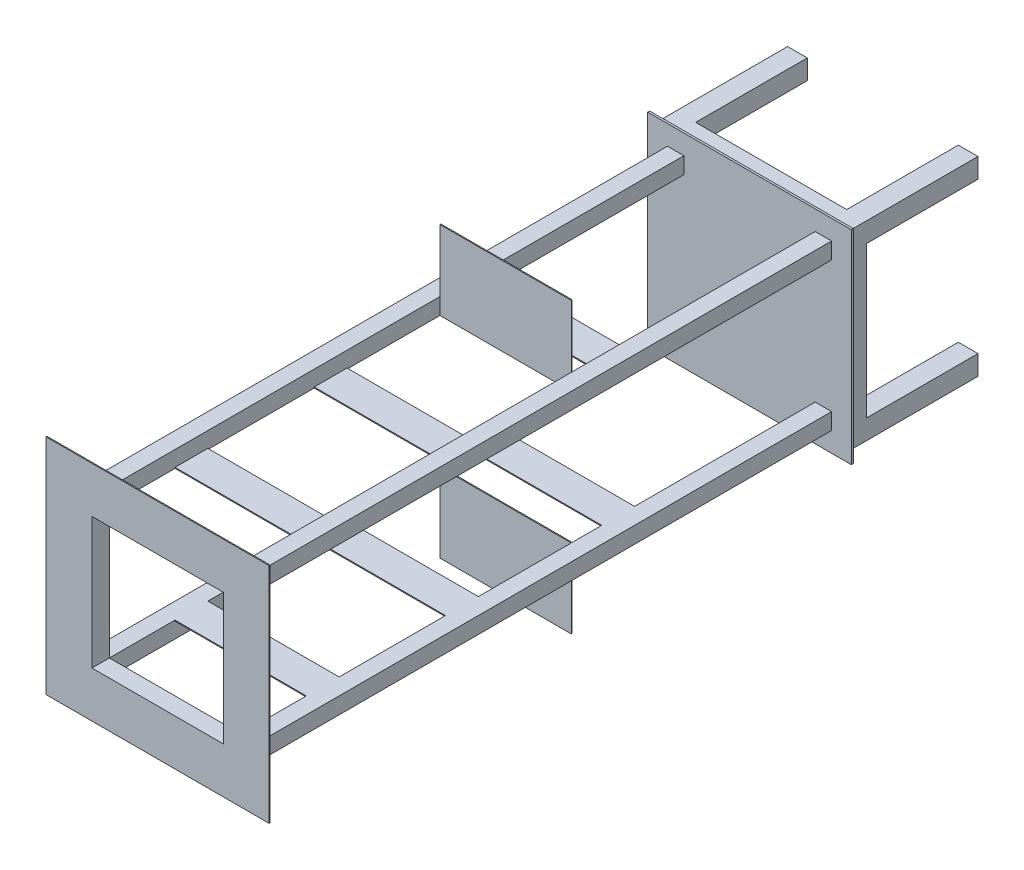
SolidWorks part; units mm, degrees
material "可鍛鑄鐵"
ref_plane "前基準面" through (0, 0, 0) normal (0, 0, 1) x (1, 0, 0)
ref_plane "上基準面" through (0, 0, 0) normal (0, 1, 0) x (1, 0, 0)
ref_plane "右基準面" through (0, 0, 0) normal (1, 0, 0) x (0, 0, -1)
other "質量中心"
sketch "草圖1" plane through (0, 0, 0) normal (0, 0, 1) x (1, 0, 0)
  line L0 (-96.0687, 115.7874) -> (-70.0687, 115.7874)
  line L1 (-98.0687, 117.7874) -> (-68.0687, 117.7874)
  line L2 (-98.0687, 117.7874) -> (-98.0687, 87.7874)
  line L3 (-98.0687, 87.7874) -> (-68.0687, 87.7874)
  line L4 (-68.0687, 117.7874) -> (-68.0687, 87.7874)
  line L5 (-70.0687, 115.7874) -> (-70.0687, 89.7874)
  line L6 (-96.0687, 89.7874) -> (-70.0687, 89.7874)
  line L7 (-96.0687, 115.7874) -> (-96.0687, 89.7874)
  line L8 (163.9313, 115.7874) -> (189.9313, 115.7874)
  line L9 (161.9313, 117.7874) -> (191.9313, 117.7874)
  line L10 (161.9313, 117.7874) -> (161.9313, 87.7874)
  line L11 (161.9313, 87.7874) -> (191.9313, 87.7874)
  line L12 (191.9313, 117.7874) -> (191.9313, 87.7874)
  line L13 (189.9313, 115.7874) -> (189.9313, 89.7874)
  line L14 (163.9313, 89.7874) -> (189.9313, 89.7874)
  line L15 (163.9313, 115.7874) -> (163.9313, 89.7874)
  line L16 (163.9313, -144.2126) -> (189.9313, -144.2126)
  line L17 (-98.0687, -142.2126) -> (-68.0687, -142.2126)
  line L18 (-98.0687, -142.2126) -> (-98.0687, -172.2126)
  line L19 (-98.0687, -172.2126) -> (-68.0687, -172.2126)
  line L20 (-68.0687, -142.2126) -> (-68.0687, -172.2126)
  line L21 (161.9313, -142.2126) -> (191.9313, -142.2126)
  line L22 (161.9313, -142.2126) -> (161.9313, -172.2126)
  line L23 (161.9313, -172.2126) -> (191.9313, -172.2126)
  line L24 (191.9313, -142.2126) -> (191.9313, -172.2126)
  line L25 (189.9313, -144.2126) -> (189.9313, -170.2126)
  line L26 (163.9313, -170.2126) -> (189.9313, -170.2126)
  line L27 (163.9313, -144.2126) -> (163.9313, -170.2126)
  line L28 (-96.0687, -144.2126) -> (-70.0687, -144.2126)
  line L29 (-70.0687, -144.2126) -> (-70.0687, -170.2126)
  line L30 (-96.0687, -170.2126) -> (-70.0687, -170.2126)
  line L31 (-96.0687, -144.2126) -> (-96.0687, -170.2126)
  point P32 (161.9313, -157.2126)
  dimension "D1" = 30
  dimension "D2" = 30
  dimension "D4" = 30
  dimension "D5" = 30
  dimension "D7" = 230
  dimension "D8" = 30
  dimension "D9" = 30
  dimension "D10" = 30
  dimension "30" = 30
  dimension "D13" = 230
  dimension "D14" = 230
  dimension "D15" = 230
  dimension "D16" = 0
  dimension "D3" = 2
  dimension "D6" = 2
  dimension "D11" = 2
  dimension "D12" = 2
extrude "填料-伸長1" add sketch "草圖1" along normal blind 200 contours L11 L12 L9 L10 | L14 L13 L8 L15 | L23 L24 L21 L22 | L6 L5 L0 L7 | L3 L4 L1 L2 | L25 L26 L27 L16 | L17 L20 L19 L18 | L28 L29 L30 L31
sketch "草圖2" plane through (0, 0, 200) normal (0, 0, 1) x (1, 0, 0)
  line L0 (-98.0687, 117.7874) -> (-98.0687, 87.7874) construction
  line L1 (-108.0687, 127.7874) -> (201.9313, 127.7874)
  line L2 (-108.0687, 127.7874) -> (-108.0687, -182.2126)
  line L3 (-108.0687, -182.2126) -> (201.9313, -182.2126)
  line L4 (201.9313, 127.7874) -> (201.9313, -182.2126)
  line L5 (-98.0687, 117.7874) -> (-68.0687, 117.7874) construction
  line L6 (191.9313, -142.2126) -> (191.9313, -172.2126) construction
  line L7 (161.9313, -172.2126) -> (191.9313, -172.2126) construction
  dimension "D1" = 10
  dimension "D2" = 10
  dimension "D3" = 10
  dimension "D4" = 10
extrude "填料-伸長2" add sketch "草圖2" along normal blind 3
sketch "草圖5" plane through (0, 0, 203) normal (0, 0, 1) x (1, 0, 0)
  line L0 (-76.5687, 96.2874) -> (-54.5687, 96.2874)
  line L1 (-78.0687, 97.7874) -> (-53.0687, 97.7874)
  line L2 (-78.0687, 97.7874) -> (-78.0687, 72.7874)
  line L3 (-78.0687, 72.7874) -> (-53.0687, 72.7874)
  line L4 (-53.0687, 97.7874) -> (-53.0687, 72.7874)
  line L5 (-54.5687, 96.2874) -> (-54.5687, 74.2874)
  line L6 (-76.5687, 74.2874) -> (-54.5687, 74.2874)
  line L7 (-76.5687, 96.2874) -> (-76.5687, 74.2874)
  line L8 (-76.5687, -128.7126) -> (-54.5687, -128.7126)
  line L9 (-78.0687, -127.2126) -> (-53.0687, -127.2126)
  line L10 (-78.0687, -127.2126) -> (-78.0687, -152.2126)
  line L11 (-78.0687, -152.2126) -> (-53.0687, -152.2126)
  line L12 (-53.0687, -127.2126) -> (-53.0687, -152.2126)
  line L13 (-54.5687, -128.7126) -> (-54.5687, -150.7126)
  line L14 (-76.5687, -150.7126) -> (-54.5687, -150.7126)
  line L15 (-76.5687, -128.7126) -> (-76.5687, -150.7126)
  line L16 (-108.0687, -182.2126) -> (201.9313, -182.2126) construction
  line L17 (-108.0687, 127.7874) -> (-108.0687, -182.2126) construction
  line L18 (46.9313, 127.7874) -> (46.9313, -191.9182) construction
  line L19 (201.9313, 127.7874) -> (-108.0687, 127.7874) construction
  line L20 (170.4313, -128.7126) -> (170.4313, -150.7126)
  line L21 (170.4313, -150.7126) -> (148.4313, -150.7126)
  line L22 (148.4313, -128.7126) -> (148.4313, -150.7126)
  line L23 (146.9313, -127.2126) -> (146.9313, -152.2126)
  line L24 (171.9313, -152.2126) -> (146.9313, -152.2126)
  line L25 (171.9313, -127.2126) -> (171.9313, -152.2126)
  line L26 (171.9313, -127.2126) -> (146.9313, -127.2126)
  line L27 (170.4313, -128.7126) -> (148.4313, -128.7126)
  line L28 (170.4313, 96.2874) -> (170.4313, 74.2874)
  line L29 (170.4313, 74.2874) -> (148.4313, 74.2874)
  line L30 (148.4313, 96.2874) -> (148.4313, 74.2874)
  line L31 (146.9313, 97.7874) -> (146.9313, 72.7874)
  line L32 (171.9313, 72.7874) -> (146.9313, 72.7874)
  line L33 (171.9313, 97.7874) -> (171.9313, 72.7874)
  line L34 (171.9313, 97.7874) -> (146.9313, 97.7874)
  line L35 (170.4313, 96.2874) -> (148.4313, 96.2874)
  dimension "D1" = 25
  dimension "D2" = 25
  dimension "D4" = 25
  dimension "D5" = 25
  dimension "D7" = 250
  dimension "D8" = 30
  dimension "D9" = 30
  dimension "D10" = 30
  dimension "D3" = 1.5
  dimension "D6" = 1.5
extrude "填料-伸長3" add sketch "草圖5" along normal blind 900 contours L4 L1 L2 L3 L7 L0 L5 L6 | L13 L14 L15 L8 | L12 L11 L10 L9 | L20 L21 L22 L27 | L25 L24 L23 L26 | L28 L29 L30 L35 | L33 L32 L31 L34
sketch "草圖6" plane through (0, 0, 1103) normal (0, 0, 1) x (1, 0, 0)
  line L1 (-123.0687, 142.7874) -> (216.9313, 142.7874)
  line L2 (-123.0687, 142.7874) -> (-123.0687, -197.2126)
  line L3 (-123.0687, -197.2126) -> (216.9313, -197.2126)
  line L4 (216.9313, 142.7874) -> (216.9313, -197.2126)
  line L5 (-53.0687, 72.7874) -> (146.9313, 72.7874)
  line L6 (-53.0687, 72.7874) -> (-53.0687, -127.2126)
  line L7 (-53.0687, -127.2126) -> (146.9313, -127.2126)
  line L8 (146.9313, 72.7874) -> (146.9313, -127.2126)
  dimension "D2" = 70
  dimension "D3" = 70
  dimension "D4" = 70
  dimension "70" = 70
extrude "填料-伸長4" add sketch "草圖6" along normal blind 1.5
ref_plane "平面1" through (0, 0, 573) normal (0, 0, 1) x (1, 0, 0)
sketch "草圖7" plane through (0, 0, 573) normal (0, 0, 1) x (1, 0, 0)
  line L1 (-53.0687, 72.7874) -> (146.9313, 72.7874)
  line L2 (-53.0687, 72.7874) -> (-53.0687, 192.7874)
  line L3 (-53.0687, 192.7874) -> (146.9313, 192.7874)
  line L4 (146.9313, 72.7874) -> (146.9313, 192.7874)
  line L6 (146.9313, -127.2126) -> (-53.0687, -127.2126)
  line L7 (146.9313, -127.2126) -> (146.9313, -247.2126)
  line L8 (146.9313, -247.2126) -> (-53.0687, -247.2126)
  line L9 (-53.0687, -127.2126) -> (-53.0687, -247.2126)
  line L10 (-53.0687, 72.7874) -> (-53.0687, -127.2126) construction
  line L13 (146.9313, -127.2126) -> (146.9313, 72.7874) construction
  line L14 (-53.0687, -127.2126) -> (146.9313, -127.2126) construction
  dimension "D1" = 0
  dimension "D2" = 0
  dimension "D3" = 0
  dimension "D4" = 0
  dimension "D5" = 0
  dimension "D6" = 120
  dimension "D7" = 120
extrude "填料-伸長5" add sketch "草圖7" along normal blind 1.5
ref_plane "平面2" through (0, 0, 953) normal (0, 0, -1) x (-1, 0, 0)
ref_plane "平面3" through (0, 0, 503) normal (0, 0, -1) x (-1, 0, 0)
ref_plane "平面5" through (0, 0, 741) normal (0, 0, -1) x (-1, 0, 0)
sketch "草圖8" plane through (0, 0, 953) normal (0, 0, -1) x (-1, 0, 0)
  line L0 (-146.9313, 72.7874) -> (53.0687, 72.7874) construction
  line L1 (-146.9313, 72.7874) -> (53.0687, 72.7874)
  line L2 (-146.9313, 72.7874) -> (-146.9313, 74.2874)
  line L3 (-146.9313, 74.2874) -> (53.0687, 74.2874)
  line L4 (53.0687, 72.7874) -> (53.0687, 74.2874)
  line L6 (-146.9313, -127.2126) -> (53.0687, -127.2126)
  line L7 (-146.9313, -127.2126) -> (-146.9313, -128.7126)
  line L8 (-146.9313, -128.7126) -> (53.0687, -128.7126)
  line L9 (53.0687, -127.2126) -> (53.0687, -128.7126)
  line L11 (53.0687, -127.2126) -> (-146.9313, -127.2126) construction
  line L12 (53.0687, 72.7874) -> (53.0687, -127.2126) construction
  line L13 (-146.9313, -127.2126) -> (-146.9313, 72.7874) construction
  dimension "D1" = 1.5
  dimension "D2" = 1.5
  dimension "D3" = 0
  dimension "D4" = 0
  dimension "D5" = 0
  dimension "D6" = 0
  dimension "D7" = 0
  dimension "D8" = 0
extrude "填料-伸長6" add sketch "草圖8" along normal mid plane 50
sketch "草圖9" plane through (0, 0, 741) normal (0, 0, -1) x (-1, 0, 0)
  line L1 (53.0687, 72.7874) -> (-146.9313, 72.7874)
  line L2 (53.0687, 72.7874) -> (53.0687, 74.2874)
  line L3 (53.0687, 74.2874) -> (-146.9313, 74.2874)
  line L4 (-146.9313, 72.7874) -> (-146.9313, 74.2874)
  line L5 (53.0687, -127.2126) -> (-146.9313, -127.2126)
  line L6 (53.0687, -127.2126) -> (53.0687, -128.7126)
  line L7 (53.0687, -128.7126) -> (-146.9313, -128.7126)
  line L8 (-146.9313, -127.2126) -> (-146.9313, -128.7126)
  dimension "D1" = 1.5
  dimension "D2" = 1.5
extrude "填料-伸長7" add sketch "草圖9" along normal mid plane 50
sketch "草圖11" plane through (0, 0, 503) normal (0, 0, -1) x (-1, 0, 0)
  line L1 (53.0687, -127.2126) -> (-146.9313, -127.2126)
  line L2 (53.0687, -127.2126) -> (53.0687, -128.7126)
  line L3 (53.0687, -128.7126) -> (-146.9313, -128.7126)
  line L4 (-146.9313, -127.2126) -> (-146.9313, -128.7126)
  line L5 (53.0687, 72.7874) -> (-146.9313, 72.7874)
  line L6 (53.0687, 72.7874) -> (53.0687, 74.2874)
  line L7 (53.0687, 74.2874) -> (-146.9313, 74.2874)
  line L8 (-146.9313, 72.7874) -> (-146.9313, 74.2874)
  dimension "D1" = 1.5
  dimension "D2" = 1.5
extrude "填料-伸長8" add sketch "草圖11" along normal mid plane 50
sketch "草圖12" plane through (-68.0687, 0, 0) normal (1, 0, 0) x (0, 0, -1)
  line L0 (-200, 117.7874) -> (0, 117.7874) construction
  line L1 (-200, 87.7874) -> (-170, 87.7874)
  line L2 (-200, 87.7874) -> (-200, 117.7874)
  line L3 (-200, 117.7874) -> (-170, 117.7874)
  line L4 (-170, 87.7874) -> (-170, 117.7874)
  line L5 (-200, -142.2126) -> (0, -142.2126) construction
  line L6 (-200, -172.2126) -> (-170, -172.2126)
  line L7 (-200, -172.2126) -> (-200, -142.2126)
  line L8 (-200, -142.2126) -> (-170, -142.2126)
  line L9 (-170, -172.2126) -> (-170, -142.2126)
  dimension "D1" = 30
  dimension "D2" = 30
extrude "填料-伸長9" add sketch "草圖12" along normal blind 230
sketch "草圖13" plane through (0, -142.2126, 0) normal (0, 1, 0) x (1, 0, 0)
  line L1 (-68.0687, -170) -> (-98.0687, -170)
  line L2 (-68.0687, -170) -> (-68.0687, -200)
  line L3 (-68.0687, -200) -> (-98.0687, -200)
  line L4 (-98.0687, -170) -> (-98.0687, -200)
  line L5 (161.9313, -170) -> (191.9313, -170)
  line L6 (161.9313, -170) -> (161.9313, -200)
  line L7 (161.9313, -200) -> (191.9313, -200)
  line L8 (191.9313, -170) -> (191.9313, -200)
extrude "填料-伸長10" add sketch "草圖13" along normal blind 230
sketch "草圖14" plane through (0, -127.2126, 0) normal (0, 1, 0) x (1, 0, 0)
  line L0 (-53.0687, -1103) -> (-53.0687, -978) construction
  line L1 (-78.0687, -1103) -> (-53.0687, -1103)
  line L2 (-78.0687, -1103) -> (-78.0687, -1078)
  line L3 (-78.0687, -1078) -> (-53.0687, -1078)
  line L4 (-53.0687, -1103) -> (-53.0687, -1078)
  line L5 (171.9313, -1103) -> (171.9313, -203) construction
  line L6 (146.9313, -1103) -> (171.9313, -1103)
  line L7 (146.9313, -1103) -> (146.9313, -1078)
  line L8 (146.9313, -1078) -> (171.9313, -1078)
  line L9 (171.9313, -1103) -> (171.9313, -1078)
  dimension "D1" = 25
extrude "填料-伸長11" add sketch "草圖14" along normal blind 220
sketch "草圖15" plane through (-53.0687, 0, 0) normal (1, 0, 0) x (0, 0, -1)
  line L1 (-1078, 72.7874) -> (-1103, 72.7874)
  line L2 (-1078, 72.7874) -> (-1078, 97.7874)
  line L3 (-1078, 97.7874) -> (-1103, 97.7874)
  line L4 (-1103, 72.7874) -> (-1103, 97.7874)
  line L5 (-1078, -127.2126) -> (-1103, -127.2126)
  line L6 (-1078, -127.2126) -> (-1078, -152.2126)
  line L7 (-1078, -152.2126) -> (-1103, -152.2126)
  line L8 (-1103, -127.2126) -> (-1103, -152.2126)
extrude "填料-伸長12" add sketch "草圖15" along normal blind 220
